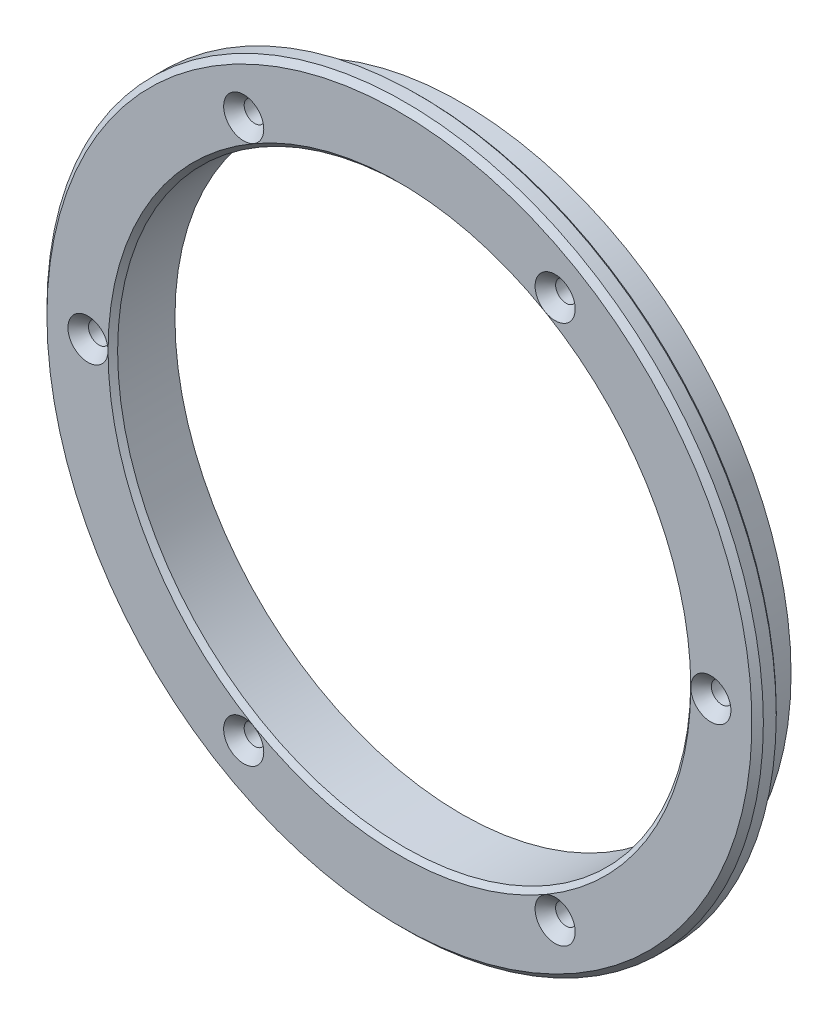
SolidWorks part; units mm, degrees
ref_plane "Front Plane" through (0, 0, 0) normal (0, 0, 1) x (1, 0, 0)
ref_plane "Top Plane" through (0, 0, 0) normal (0, 1, 0) x (1, 0, 0)
ref_plane "Right Plane" through (0, 0, 0) normal (1, 0, 0) x (0, 0, -1)
ref_plane "Plane1" through (0, 0, 12.7) normal (0, 0, 1) x (1, 0, 0)
sketch "Sketch1" plane through (0, 0, 12.7) normal (0, 0, 1) x (1, 0, 0)
  circle A0 centre (0, 0) radius 47.625
extrude "Extrude1" add sketch "Sketch1" against normal blind 8.255
sketch "Sketch2" plane through (0, 0, 12.7) normal (0, 0, 1) x (1, 0, 0)
  circle A0 centre (0, 0) radius 38.1
extrude "Extrude2" cut sketch "Sketch2" against normal blind 8.255
ref_plane "Plane2" through (0, 0, 0) normal (0, -1, 0) x (1, 0, 0)
sketch "Sketch3" plane through (0, 0, 0) normal (0, -1, 0) x (1, 0, 0)
  line L0 (47.625, 4.445) -> (47.625, 9.8425)
  line L1 (47.625, 9.8425) -> (43.815, 9.8425)
  line L2 (43.815, 9.8425) -> (43.815, 4.445)
  line L3 (43.815, 4.445) -> (47.625, 4.445)
  line L4 (0, 9.8425) -> (0, 4.445) construction
revolve "Cut-Revolve1" cut sketch "Sketch3" angle 360 about L4
chamfer "Chamfer1" distance 0.635 angle 45 1 edges at (-38.1, 0, 12.7)
hole_wizard "Hole1" positions "Sketch5" profile "Sketch4" legacy
sketch "Sketch5" plane through (0, 0, 12.7) normal (0, 0, 1) x (1, 0, 0)
  point P0 (-20.701, -35.8552)
sketch "Sketch4" plane through (-20.701, -35.8552, 12.7) normal (1, 0, 0) x (0, -1, 0)
  line L0 (0, 0) -> (0, 8.255)
  line L1 (0, 8.255) -> (1.397, 8.255)
  line L2 (1.397, 8.255) -> (1.397, 1.461)
  line L3 (1.397, 1.461) -> (2.667, 0)
  line L4 (2.667, 0) -> (0, 0)
  line L5 (0, -6.4453) -> (0, 115.525) construction
  line L6 (-1.397, 1.461) -> (-2.667, 0) construction
  dimension "Diameter" = 2.794
  dimension "Depth" = 8.255
  dimension "C-Sink Angle" = 82
  dimension "C-Sink Diameter" = 5.334
hole_wizard "Hole2" positions "Sketch7" profile "Sketch6" legacy
sketch "Sketch7" plane through (0, 0, 12.7) normal (0, 0, 1) x (1, 0, 0)
  point P0 (-41.402, 0)
sketch "Sketch6" plane through (-41.402, 0, 12.7) normal (1, 0, 0) x (0, -1, 0)
  line L0 (0, 0) -> (0, 8.255)
  line L1 (0, 8.255) -> (1.397, 8.255)
  line L2 (1.397, 8.255) -> (1.397, 1.461)
  line L3 (1.397, 1.461) -> (2.667, 0)
  line L4 (2.667, 0) -> (0, 0)
  line L5 (0, -6.4453) -> (0, 115.525) construction
  line L6 (-1.397, 1.461) -> (-2.667, 0) construction
  dimension "Diameter" = 2.794
  dimension "Depth" = 8.255
  dimension "C-Sink Angle" = 82
  dimension "C-Sink Diameter" = 5.334
hole_wizard "Hole3" positions "Sketch9" profile "Sketch8" legacy end condition up to next
sketch "Sketch9" plane through (0, 0, 12.7) normal (0, 0, 1) x (1, 0, 0)
  point P0 (-20.701, 35.8552)
sketch "Sketch8" plane through (-20.701, 35.8552, 12.7) normal (1, 0, 0) x (0, -1, 0)
  line L0 (0, 0) -> (0, 8.255)
  line L1 (0, 8.255) -> (1.397, 8.255)
  line L2 (1.397, 8.255) -> (1.397, 1.461)
  line L3 (1.397, 1.461) -> (2.667, 0)
  line L4 (2.667, 0) -> (0, 0)
  line L5 (0, -6.4453) -> (0, 115.525) construction
  line L6 (-1.397, 1.461) -> (-2.667, 0) construction
  dimension "Diameter" = 2.794
  dimension "Depth" = 8.255
  dimension "C-Sink Angle" = 82
  dimension "C-Sink Diameter" = 5.334
hole_wizard "Hole4" positions "Sketch11" profile "Sketch10" legacy
sketch "Sketch11" plane through (0, 0, 12.7) normal (0, 0, 1) x (1, 0, 0)
  point P0 (20.701, 35.8552)
sketch "Sketch10" plane through (20.701, 35.8552, 12.7) normal (1, 0, 0) x (0, -1, 0)
  line L0 (0, 0) -> (0, 8.255)
  line L1 (0, 8.255) -> (1.397, 8.255)
  line L2 (1.397, 8.255) -> (1.397, 1.461)
  line L3 (1.397, 1.461) -> (2.667, 0)
  line L4 (2.667, 0) -> (0, 0)
  line L5 (0, -6.4453) -> (0, 115.525) construction
  line L6 (-1.397, 1.461) -> (-2.667, 0) construction
  dimension "Diameter" = 2.794
  dimension "Depth" = 8.255
  dimension "C-Sink Angle" = 82
  dimension "C-Sink Diameter" = 5.334
hole_wizard "Hole5" positions "Sketch13" profile "Sketch12" legacy
sketch "Sketch13" plane through (0, 0, 12.7) normal (0, 0, 1) x (1, 0, 0)
  point P0 (20.701, -35.8552)
sketch "Sketch12" plane through (20.701, -35.8552, 12.7) normal (1, 0, 0) x (0, -1, 0)
  line L0 (0, 0) -> (0, 8.255)
  line L1 (0, 8.255) -> (1.397, 8.255)
  line L2 (1.397, 8.255) -> (1.397, 1.461)
  line L3 (1.397, 1.461) -> (2.667, 0)
  line L4 (2.667, 0) -> (0, 0)
  line L5 (0, -6.4453) -> (0, 115.525) construction
  line L6 (-1.397, 1.461) -> (-2.667, 0) construction
  dimension "Diameter" = 2.794
  dimension "Depth" = 8.255
  dimension "C-Sink Angle" = 82
  dimension "C-Sink Diameter" = 5.334
hole_wizard "Hole6" positions "Sketch15" profile "Sketch14" legacy
sketch "Sketch15" plane through (0, 0, 12.7) normal (0, 0, 1) x (1, 0, 0)
  point P0 (41.402, 0)
sketch "Sketch14" plane through (41.402, 0, 12.7) normal (1, 0, 0) x (0, -1, 0)
  line L0 (0, 0) -> (0, 8.255)
  line L1 (0, 8.255) -> (1.397, 8.255)
  line L2 (1.397, 8.255) -> (1.397, 1.461)
  line L3 (1.397, 1.461) -> (2.667, 0)
  line L4 (2.667, 0) -> (0, 0)
  line L5 (0, -6.4453) -> (0, 115.525) construction
  line L6 (-1.397, 1.461) -> (-2.667, 0) construction
  dimension "Diameter" = 2.794
  dimension "Depth" = 8.255
  dimension "C-Sink Angle" = 82
  dimension "C-Sink Diameter" = 5.334
chamfer "Chamfer2" distance 0.381 angle 45 1 edges at (-47.625, 0, 9.8425)
chamfer "Chamfer3" distance 0.762 angle 45 1 edges at (-47.625, 0, 12.7)
